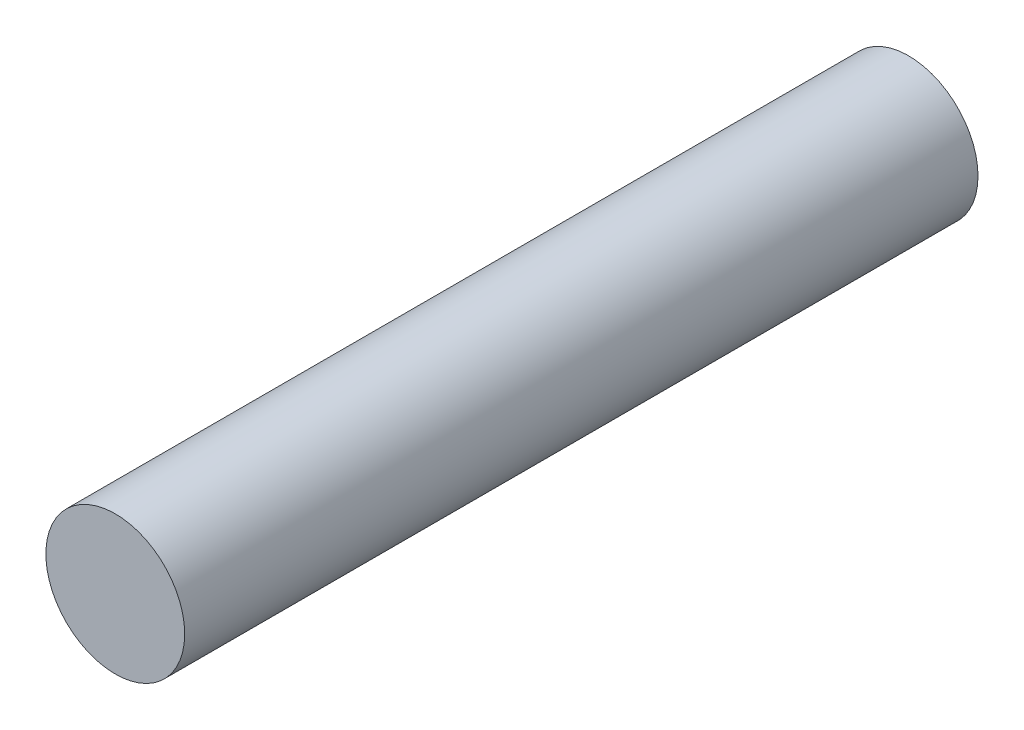
SolidWorks part; units mm, degrees
ref_plane "Ön Düzlem" through (0, 0, 0) normal (0, 0, 1) x (1, 0, 0)
ref_plane "Üst Düzlem" through (0, 0, 0) normal (0, 1, 0) x (1, 0, 0)
ref_plane "Sağ Düzlem" through (0, 0, 0) normal (1, 0, 0) x (0, 0, -1)
sketch "Çizim1" plane through (0, 0, 0) normal (0, 0, 1) x (1, 0, 0)
  circle A0 centre (0, 0) radius 3.5
  dimension "D1" = 7
extrude "Yükseklik-Ekstrüzyon1" add sketch "Çizim1" along normal blind 40
